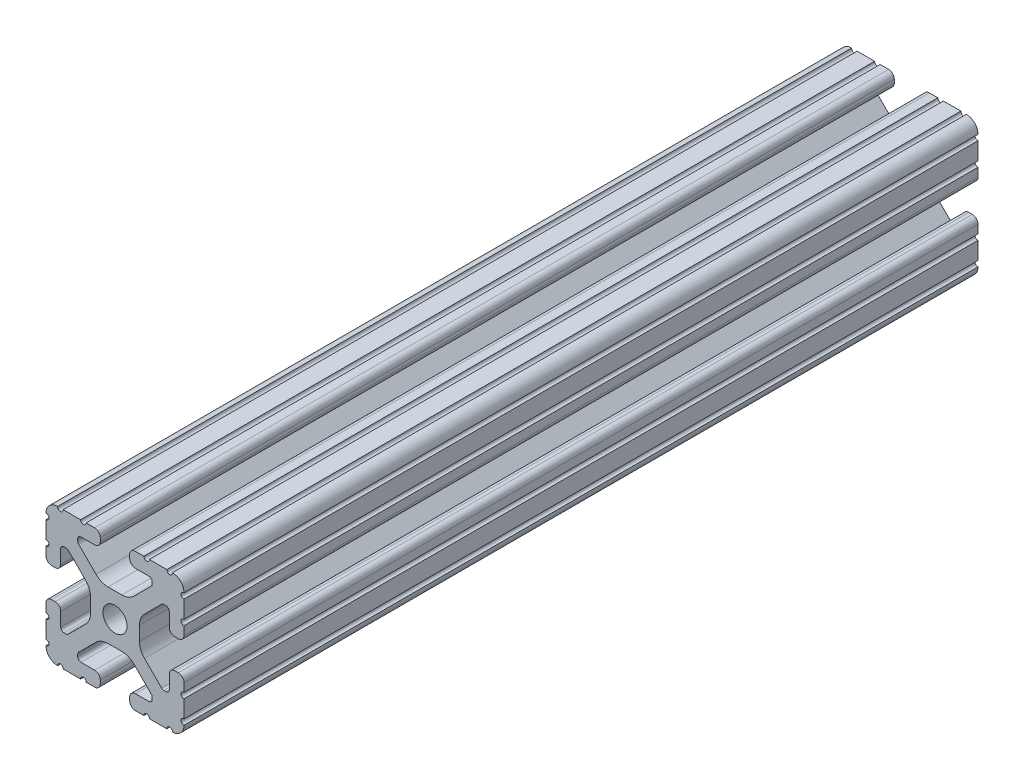
SolidWorks part; units mm, degrees
ref_plane "Front" through (0, 0, 0) normal (0, 0, 1) x (1, 0, 0)
ref_plane "Top" through (0, 0, 0) normal (0, 1, 0) x (1, 0, 0)
ref_plane "Right" through (0, 0, 0) normal (1, 0, 0) x (0, 0, -1)
sketch "Sketch1" plane through (0, 0, 0) normal (0, 0, 1) x (1, 0, 0)
  line L104 (-10.287, 13.5524) -> (-10.287, 14.0843)
  line L105 (-9.3853, 14.986) -> (-5.6176, 14.986)
  line L106 (-4.064, 16.5396) -> (-4.064, 17.4964)
  line L107 (-5.6176, 19.05) -> (-7.9742, 19.05)
  line L108 (-9.4982, 19.05) -> (-14.3277, 19.05)
  line L109 (-19.05, 14.3277) -> (-19.05, 9.4961)
  line L110 (-19.05, 7.9763) -> (-19.05, 5.6176)
  line L111 (-17.4964, 4.064) -> (-16.5396, 4.064)
  line L112 (-14.986, 5.6176) -> (-14.986, 9.3853)
  line L113 (-14.0843, 10.287) -> (-13.516, 10.287)
  line L114 (-12.8784, 10.0229) -> (-8.1476, 5.2921)
  line L115 (-6.7564, 1.9335) -> (-6.7564, -1.9335)
  line L116 (-8.1476, -5.2921) -> (-12.8784, -10.0229)
  line L117 (-13.516, -10.287) -> (-14.0843, -10.287)
  line L118 (-14.986, -9.3853) -> (-14.986, -5.6176)
  line L119 (-16.5396, -4.064) -> (-17.4964, -4.064)
  line L120 (-19.05, -5.6176) -> (-19.05, -7.9763)
  line L121 (-19.05, -9.4961) -> (-19.05, -14.3277)
  line L122 (-14.3277, -19.05) -> (-9.4961, -19.05)
  line L123 (-7.9763, -19.05) -> (-5.6176, -19.05)
  line L124 (-4.064, -17.4964) -> (-4.064, -16.5396)
  line L125 (-5.6176, -14.986) -> (-9.3853, -14.986)
  line L126 (-10.287, -14.0843) -> (-10.287, -13.5524)
  line L127 (-10.0229, -12.9148) -> (-5.2522, -8.144)
  line L128 (-1.9022, -6.7564) -> (1.9022, -6.7564)
  line L129 (5.2522, -8.144) -> (10.0229, -12.9148)
  line L130 (10.287, -13.5524) -> (10.287, -14.0843)
  line L131 (9.3853, -14.986) -> (5.6176, -14.986)
  line L132 (4.064, -16.5396) -> (4.064, -17.4964)
  line L133 (5.6176, -19.05) -> (7.9763, -19.05)
  line L134 (9.4961, -19.05) -> (14.3277, -19.05)
  line L135 (19.05, -14.3277) -> (19.05, -9.4961)
  line L136 (19.05, -7.9763) -> (19.05, -5.6176)
  line L137 (17.4964, -4.064) -> (16.5396, -4.064)
  line L138 (14.986, -5.6176) -> (14.986, -9.3853)
  line L139 (14.0843, -10.287) -> (13.516, -10.287)
  line L140 (12.8784, -10.0229) -> (8.1476, -5.2921)
  line L141 (6.7564, -1.9335) -> (6.7564, 1.9335)
  line L142 (8.1476, 5.2921) -> (12.8784, 10.0229)
  line L143 (13.516, 10.287) -> (14.0843, 10.287)
  line L144 (14.986, 9.3853) -> (14.986, 5.6176)
  line L145 (16.5396, 4.064) -> (17.4964, 4.064)
  line L146 (19.05, 5.6176) -> (19.05, 7.9763)
  line L147 (19.05, 9.4961) -> (19.05, 14.3277)
  line L148 (14.3277, 19.05) -> (9.4982, 19.05)
  line L149 (7.9742, 19.05) -> (5.6176, 19.05)
  line L150 (4.064, 17.4964) -> (4.064, 16.5396)
  line L151 (5.6176, 14.986) -> (9.3853, 14.986)
  line L152 (10.287, 14.0843) -> (10.287, 13.5524)
  line L153 (10.0229, 12.9148) -> (5.2522, 8.144)
  line L154 (1.9022, 6.7564) -> (-1.9022, 6.7564)
  line L155 (-5.2522, 8.144) -> (-10.0229, 12.9148)
  circle A1 centre (0, 0) radius 3.3274
  arc A120 (-9.3853, 14.986) -> (-10.287, 14.0843) centre (-9.3853, 14.0843) ccw
  arc A121 (-5.6176, 14.986) -> (-4.064, 16.5396) centre (-5.6176, 16.5396) ccw
  arc A122 (-4.064, 17.4964) -> (-5.6176, 19.05) centre (-5.6176, 17.4964) ccw
  arc A123 (-9.4982, 19.05) -> (-7.9742, 19.05) centre (-8.7362, 19.05) ccw
  arc A124 (-15.8475, 19.05) -> (-14.3277, 19.05) centre (-15.0876, 18.9933) ccw
  arc A125 (-15.8475, 19.05) -> (-19.05, 15.8475) centre (-15.8751, 15.8751) ccw
  arc A126 (-19.05, 14.3277) -> (-19.05, 15.8475) centre (-18.9933, 15.0876) ccw
  arc A127 (-19.05, 7.9763) -> (-19.05, 9.4961) centre (-18.9933, 8.7362) ccw
  arc A128 (-19.05, 5.6176) -> (-17.4964, 4.064) centre (-17.4964, 5.6176) ccw
  arc A129 (-16.5396, 4.064) -> (-14.986, 5.6176) centre (-16.5396, 5.6176) ccw
  arc A130 (-14.0843, 10.287) -> (-14.986, 9.3853) centre (-14.0843, 9.3853) ccw
  arc A131 (-12.8784, 10.0229) -> (-13.516, 10.287) centre (-13.516, 9.3853) ccw
  arc A132 (-6.7564, 1.9335) -> (-8.1476, 5.2921) centre (-11.5062, 1.9335) ccw
  arc A133 (-8.1476, -5.2921) -> (-6.7564, -1.9335) centre (-11.5062, -1.9335) ccw
  arc A134 (-13.516, -10.287) -> (-12.8784, -10.0229) centre (-13.516, -9.3853) ccw
  arc A135 (-14.986, -9.3853) -> (-14.0843, -10.287) centre (-14.0843, -9.3853) ccw
  arc A136 (-14.986, -5.6176) -> (-16.5396, -4.064) centre (-16.5396, -5.6176) ccw
  arc A137 (-17.4964, -4.064) -> (-19.05, -5.6176) centre (-17.4964, -5.6176) ccw
  arc A138 (-19.05, -9.4961) -> (-19.05, -7.9763) centre (-18.9933, -8.7362) ccw
  arc A139 (-19.05, -15.8475) -> (-19.05, -14.3277) centre (-18.9933, -15.0876) ccw
  arc A140 (-19.05, -15.8475) -> (-15.8475, -19.05) centre (-15.8751, -15.8751) ccw
  arc A141 (-14.3277, -19.05) -> (-15.8475, -19.05) centre (-15.0876, -18.9933) ccw
  arc A142 (-7.9763, -19.05) -> (-9.4961, -19.05) centre (-8.7362, -18.9933) ccw
  arc A143 (-5.6176, -19.05) -> (-4.064, -17.4964) centre (-5.6176, -17.4964) ccw
  arc A144 (-4.064, -16.5396) -> (-5.6176, -14.986) centre (-5.6176, -16.5396) ccw
  arc A145 (-10.287, -14.0843) -> (-9.3853, -14.986) centre (-9.3853, -14.0843) ccw
  arc A146 (-10.0229, -12.9148) -> (-10.287, -13.5524) centre (-9.3853, -13.5524) ccw
  arc A147 (-1.9022, -6.7564) -> (-5.2522, -8.144) centre (-1.9022, -11.494) ccw
  arc A148 (5.2522, -8.144) -> (1.9022, -6.7564) centre (1.9022, -11.494) ccw
  arc A149 (10.287, -13.5524) -> (10.0229, -12.9148) centre (9.3853, -13.5524) ccw
  arc A150 (9.3853, -14.986) -> (10.287, -14.0843) centre (9.3853, -14.0843) ccw
  arc A151 (5.6176, -14.986) -> (4.064, -16.5396) centre (5.6176, -16.5396) ccw
  arc A152 (4.064, -17.4964) -> (5.6176, -19.05) centre (5.6176, -17.4964) ccw
  arc A153 (9.4961, -19.05) -> (7.9763, -19.05) centre (8.7362, -18.9933) ccw
  arc A154 (15.8475, -19.05) -> (14.3277, -19.05) centre (15.0876, -18.9933) ccw
  arc A155 (15.8475, -19.05) -> (19.05, -15.8475) centre (15.8751, -15.8751) ccw
  arc A156 (19.05, -14.3277) -> (19.05, -15.8475) centre (18.9933, -15.0876) ccw
  arc A157 (19.05, -7.9763) -> (19.05, -9.4961) centre (18.9933, -8.7362) ccw
  arc A158 (19.05, -5.6176) -> (17.4964, -4.064) centre (17.4964, -5.6176) ccw
  arc A159 (16.5396, -4.064) -> (14.986, -5.6176) centre (16.5396, -5.6176) ccw
  arc A160 (14.0843, -10.287) -> (14.986, -9.3853) centre (14.0843, -9.3853) ccw
  arc A161 (12.8784, -10.0229) -> (13.516, -10.287) centre (13.516, -9.3853) ccw
  arc A162 (6.7564, -1.9335) -> (8.1476, -5.2921) centre (11.5062, -1.9335) ccw
  arc A163 (8.1476, 5.2921) -> (6.7564, 1.9335) centre (11.5062, 1.9335) ccw
  arc A164 (13.516, 10.287) -> (12.8784, 10.0229) centre (13.516, 9.3853) ccw
  arc A165 (14.986, 9.3853) -> (14.0843, 10.287) centre (14.0843, 9.3853) ccw
  arc A166 (14.986, 5.6176) -> (16.5396, 4.064) centre (16.5396, 5.6176) ccw
  arc A167 (17.4964, 4.064) -> (19.05, 5.6176) centre (17.4964, 5.6176) ccw
  arc A168 (19.05, 9.4961) -> (19.05, 7.9763) centre (18.9933, 8.7362) ccw
  arc A169 (19.05, 15.8475) -> (19.05, 14.3277) centre (18.9933, 15.0876) ccw
  arc A170 (19.05, 15.8475) -> (15.8475, 19.05) centre (15.8751, 15.8751) ccw
  arc A171 (14.3277, 19.05) -> (15.8475, 19.05) centre (15.0876, 18.9933) ccw
  arc A172 (7.9742, 19.05) -> (9.4982, 19.05) centre (8.7362, 19.05) ccw
  arc A173 (5.6176, 19.05) -> (4.064, 17.4964) centre (5.6176, 17.4964) ccw
  arc A174 (4.064, 16.5396) -> (5.6176, 14.986) centre (5.6176, 16.5396) ccw
  arc A175 (10.287, 14.0843) -> (9.3853, 14.986) centre (9.3853, 14.0843) ccw
  arc A176 (10.0229, 12.9148) -> (10.287, 13.5524) centre (9.3853, 13.5524) ccw
  arc A177 (1.9022, 6.7564) -> (5.2522, 8.144) centre (1.9022, 11.494) ccw
  arc A178 (-5.2522, 8.144) -> (-1.9022, 6.7564) centre (-1.9022, 11.494) ccw
  arc A179 (-10.287, 13.5524) -> (-10.0229, 12.9148) centre (-9.3853, 13.5524) ccw
extrude "Boss-Extrude1" add sketch "Sketch1" along normal mid plane 1219.2
sketch "Sketch2" plane through (0, 19.05, 0) normal (0, 1, 0) x (1, 0, 0)
  line L0 (-52.4668, -390.329) -> (31.6825, -390.329) construction
  line L1 (21.7487, -390.329) -> (-21.0909, -390.329)
  line L2 (-21.0909, -390.329) -> (-21.0909, 611.9505)
  line L3 (-21.0909, 611.9505) -> (21.7487, 611.9505)
  line L4 (21.7487, 611.9505) -> (21.7487, -390.329)
extrude "Cut-Extrude1" cut sketch "Sketch2" against normal blind 41.148 and the other way blind 5.334
